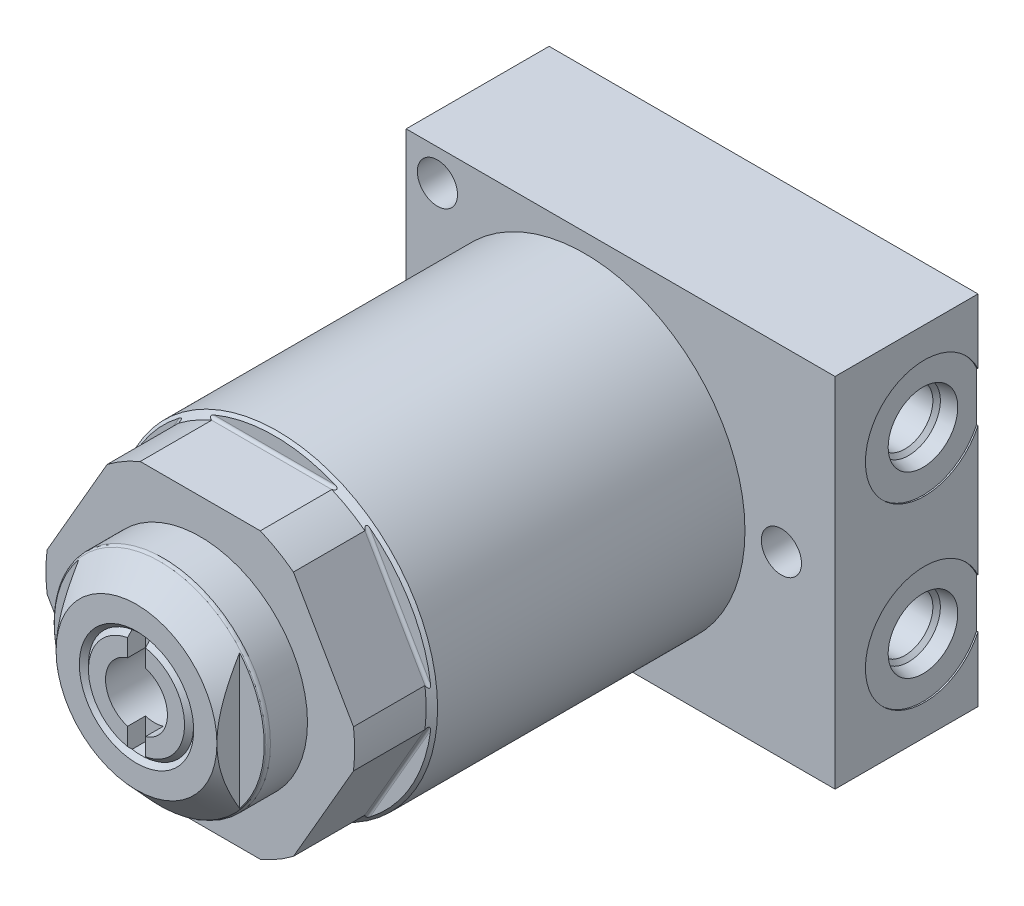
SolidWorks part; units mm, degrees
material "Alloy Steel"
ref_plane "Front Plane" through (0, 0, 0) normal (0, 0, 1) x (1, 0, 0)
ref_plane "Top Plane" through (0, 0, 0) normal (0, 1, 0) x (1, 0, 0)
ref_plane "Right Plane" through (0, 0, 0) normal (1, 0, 0) x (0, 0, -1)
ref_plane "Plane1" through (0, 0, 0) normal (0, 0, 1) x (1, 0, 0)
sketch "Sketch1" plane through (0, 0, 0) normal (0, 0, 1) x (1, 0, 0)
  circle A0 centre (0, 0) radius 28.448
  dimension "D1" = 56.896
extrude "Extrude1" add sketch "Sketch1" along normal blind 82.55
ref_plane "Plane2" through (0, 0, 0) normal (1, 0, 0) x (0, 0, 1)
sketch "Sketch2" plane through (0, 0, 0) normal (1, 0, 0) x (0, 0, 1)
  line L0 (69.342, 28.448) -> (69.342, 25.781)
  line L1 (69.85, 25.273) -> (82.55, 25.273)
  line L2 (68.6816, 0) -> (83.2104, 0) construction
  line L3 (82.55, -28.448) -> (82.55, 28.448) construction
  line L4 (69.342, 28.448) -> (82.55, 28.448)
  line L5 (82.55, 28.448) -> (82.55, 25.273)
  arc A0 (69.342, 25.781) -> (69.85, 25.273) centre (69.85, 25.781) ccw
  dimension "D3" = 0.508
  dimension "D1" = 13.208
  dimension "D2" = 50.546
extrude "Cut-Extrude1" cut sketch "Sketch2" against normal mid plane 68.2752
ref_plane "Plane12" through (0, 0, 0) normal (1, 0, 0) x (0, 0, -1)
sketch "Sketch10" plane through (0, 0, 0) normal (1, 0, 0) x (0, 0, -1)
  line L0 (-82.55, 27.432) -> (-69.85, 27.432)
  line L1 (-69.85, 27.432) -> (-68.834, 28.448)
  line L2 (-68.834, 28.448) -> (-82.55, 28.448)
  line L3 (-82.55, 28.448) -> (-82.55, 27.432)
  line L4 (-83.2358, 0) -> (-68.1482, 0) construction
  line L5 (0, 28.448) -> (-82.55, 28.448) construction
  line L6 (-82.55, 28.448) -> (-82.55, -25.273) construction
  dimension "D1" = 54.864
  dimension "D2" = 12.7
  dimension "D3" = 45
revolve "Cut-Revolve1" cut sketch "Sketch10" angle 360 about L4
ref_plane "Plane15" through (0, 0, 0) normal (1, 0, 0) x (0, 0, -1)
sketch "Sketch13" plane through (0, 0, 0) normal (1, 0, 0) x (0, 0, -1)
  line L0 (-82.55, 0) -> (-93.8784, 0)
  line L1 (-93.8784, 0) -> (-93.8784, 19.05)
  line L2 (-93.8784, 19.05) -> (-82.55, 19.05)
  line L3 (-82.55, 19.05) -> (-82.55, 0)
  line L4 (-94.4448, 0) -> (-54.8376, 0) construction
  line L5 (-82.55, 27.432) -> (-82.55, -25.273) construction
  dimension "D1" = 38.1
  dimension "D2" = 11.3284
revolve "Revolve1" add sketch "Sketch13" angle 360 about L4
ref_plane "Plane16" through (-5.4991, 0, 93.8784) normal (0, 1, 0) x (-1, 0, 0)
sketch "S2D0011" plane through (-5.4991, 0, 93.8784) normal (0, 1, 0) x (-1, 0, 0)
  line L0 (0, 0) -> (0, -16.002)
  line L1 (0, -16.002) -> (-5.4991, -16.002)
  line L2 (0, 0) -> (-5.4991, 0)
  line L3 (-5.4991, 0) -> (-5.4991, -16.002)
  line L4 (-5.4991, -54.3015) -> (-5.4991, 0.8001) construction
  line L5 (13.5509, 0) -> (-24.5491, 0) construction
  dimension "D1" = 16.002
  dimension "D2" = 10.9982
revolve "Cut-Revolve4" cut sketch "S2D0011" angle 360 about L4
ref_plane "Plane17" through (0, 0, 0) normal (1, 0, 0) x (0, 0, -1)
sketch "Sketch15" plane through (0, 0, 0) normal (1, 0, 0) x (0, 0, -1)
  line L0 (-93.8784, 14.2875) -> (-89.7066, 18.7973)
  line L1 (-94.1159, 0) -> (-59.0006, 0) construction
  line L2 (-93.8784, 19.05) -> (-93.8784, -19.05) construction
  line L3 (-82.55, 19.05) -> (-93.8784, 19.05) construction
  line L4 (-89.1286, 19.05) -> (-93.8784, 19.05)
  line L5 (-93.8784, 19.05) -> (-93.8784, 14.2875)
  arc A0 (-89.1286, 19.05) -> (-89.7066, 18.7973) centre (-89.1286, 18.2626) ccw
  dimension "D2" = 0.7874
  dimension "D1" = 28.575
  dimension "D3" = 4.7498
revolve "Cut-Revolve5" cut sketch "Sketch15" angle 360 about L1
ref_plane "Plane18" through (0, 0, 0) normal (0, 1, 0) x (-1, 0, 0)
sketch "Sketch16" plane through (0, 0, 0) normal (0, 1, 0) x (-1, 0, 0)
  line L0 (-44.45, -11.176) -> (31.75, -11.176)
  line L1 (31.75, -11.176) -> (31.75, 14.224)
  line L2 (31.75, 14.224) -> (-44.45, 14.224)
  line L3 (-44.45, 14.224) -> (-44.45, -11.176)
  line L4 (-28.448, 0) -> (28.448, 0) construction
  dimension "D1" = 76.2
  dimension "D2" = 11.176
  dimension "D3" = 25.4
  dimension "D4" = 31.75
extrude "Extrude2" add sketch "Sketch16" along normal blind 31.75 and the other way blind 31.75
sketch "Sketch17" plane through (44.45, 0, 0) normal (1, 0, 0) x (0, 0, -1)
  circle A0 centre (1.651, -15.875) radius 10.4775
extrude "Cut-Extrude9" cut sketch "Sketch17" against normal blind 0.254
sketch "Sketch18" plane through (44.45, 0, 0) normal (1, 0, 0) x (0, 0, -1)
  circle A0 centre (1.651, 15.875) radius 10.4775
extrude "Cut-Extrude10" cut sketch "Sketch18" against normal blind 0.254
ref_plane "Plane19" through (44.196, -15.875, -1.651) normal (0, 0, 1) x (0, -1, 0)
sketch "S2D0002" plane through (44.196, -15.875, -1.651) normal (0, 0, 1) x (0, -1, 0)
  line L0 (0, 0) -> (6.1849, 0)
  line L1 (6.1849, 0) -> (5.6423, -2.5527)
  line L2 (5.6423, -2.5527) -> (4.9784, -3.2166)
  line L3 (4.9784, -3.2166) -> (4.9784, -17.272)
  line L4 (4.9784, -17.272) -> (0, -17.272)
  line L5 (0, -17.272) -> (0, 0)
  line L6 (0, -18.1356) -> (0, 0.8636) construction
  dimension "D1" = 17.272
revolve "Cut-Revolve6" cut sketch "S2D0002" angle 360 about L6
ref_plane "Plane20" through (44.196, 15.875, -1.651) normal (0, 0, 1) x (0, -1, 0)
sketch "S2D0001" plane through (44.196, 15.875, -1.651) normal (0, 0, 1) x (0, -1, 0)
  line L0 (0, 0) -> (6.1849, 0)
  line L1 (6.1849, 0) -> (5.6423, -2.5527)
  line L2 (5.6423, -2.5527) -> (4.9784, -3.2166)
  line L3 (4.9784, -3.2166) -> (4.9784, -17.272)
  line L4 (4.9784, -17.272) -> (0, -17.272)
  line L5 (0, -17.272) -> (0, 0)
  line L6 (0, -18.1356) -> (0, 0.8636) construction
  dimension "D1" = 17.272
revolve "Cut-Revolve7" cut sketch "S2D0001" angle 360 about L6
pattern_circular "CirPattern2" count 6 over 360 about axis through (0, 0, 0) along (0, 0, 1) of "Cut-Extrude1"
hole_wizard "Hole1" positions "Sketch22" profile "Sketch21" legacy end condition up to next
sketch "Sketch22" plane through (0, 0, 14.224) normal (0, 0, 1) x (1, 0, 0)
  line L0 (0, 0) -> (-35.2989, 0) construction
  point P0 (-26.1874, -26.1874)
  point P1 (34.925, 0)
  point P12 (-26.1874, 26.1874)
  dimension "D1" = 34.925
  dimension "D2" = 26.1874
  dimension "D3" = 26.1874
  dimension "D4" = 52.3748
sketch "Sketch21" plane through (-26.1874, -26.1874, 14.224) normal (1, 0, 0) x (0, -1, 0)
  line L0 (0, 0) -> (0, 25.4)
  line L1 (0, 25.4) -> (3.5687, 25.4)
  line L2 (3.5687, 25.4) -> (3.5687, 0)
  line L3 (3.5687, 0) -> (0, 0)
  line L4 (0, 110) -> (0, -10) construction
  dimension "Diameter" = 7.1374
  dimension "Depth" = 25.4
sketch "Sketch23" plane through (0, 0, 93.8784) normal (0, 0, 1) x (1, 0, 0)
  line L0 (0, 0) -> (0, -35.8603) construction
  line L1 (-14.2875, 12.6004) -> (-14.2875, -12.6004)
  line L2 (14.2875, 12.6004) -> (14.2875, -12.6004)
  circle A0 centre (0, 0) radius 19.05 construction
  arc A1 (14.2875, -12.6004) -> (14.2875, 12.6004) centre (0, 0) ccw
  arc A3 (-14.2875, 12.6004) -> (-14.2875, -12.6004) centre (0, 0) ccw
  dimension "D1" = 28.575
extrude "Cut-Extrude11" cut sketch "Sketch23" against normal blind 4.0386
sketch "Sketch25" plane through (0, 0, 0) normal (1, 0, 0) x (0, 0, -1)
  line L0 (-93.8784, 8.5344) -> (-93.0656, 9.3472)
  line L1 (-93.0656, 9.3472) -> (-93.8784, 10.16)
  line L2 (-93.8784, 10.16) -> (-93.8784, 8.5344)
  line L3 (-93.1316, 0) -> (-86.5532, 0) construction
  line L5 (-93.8784, 0) -> (-93.8784, -14.2875) construction
  dimension "D1" = 9.3472
  dimension "D2" = 1.6256
  dimension "D3" = 90
  dimension "D4" = 45
revolve "Cut-Revolve8" cut sketch "Sketch25" angle 360 about L3
sketch "Sketch26" plane through (0, 0, 93.8784) normal (0, 0, 1) x (1, 0, 0)
  line L0 (0, 0) -> (0, 36.5156) construction
  line L1 (-1.5875, 9.2114) -> (-1.5875, -9.2114)
  line L2 (1.5875, 9.2114) -> (1.5875, -9.2114)
  circle A0 centre (0, 0) radius 9.3472 construction
  arc A1 (1.5875, 9.2114) -> (-1.5875, 9.2114) centre (0, 0) ccw
  arc A2 (-1.5875, -9.2114) -> (1.5875, -9.2114) centre (0, 0) ccw
  dimension "D1" = 3.175
extrude "Cut-Extrude12" cut sketch "Sketch26" against normal blind 3.175
